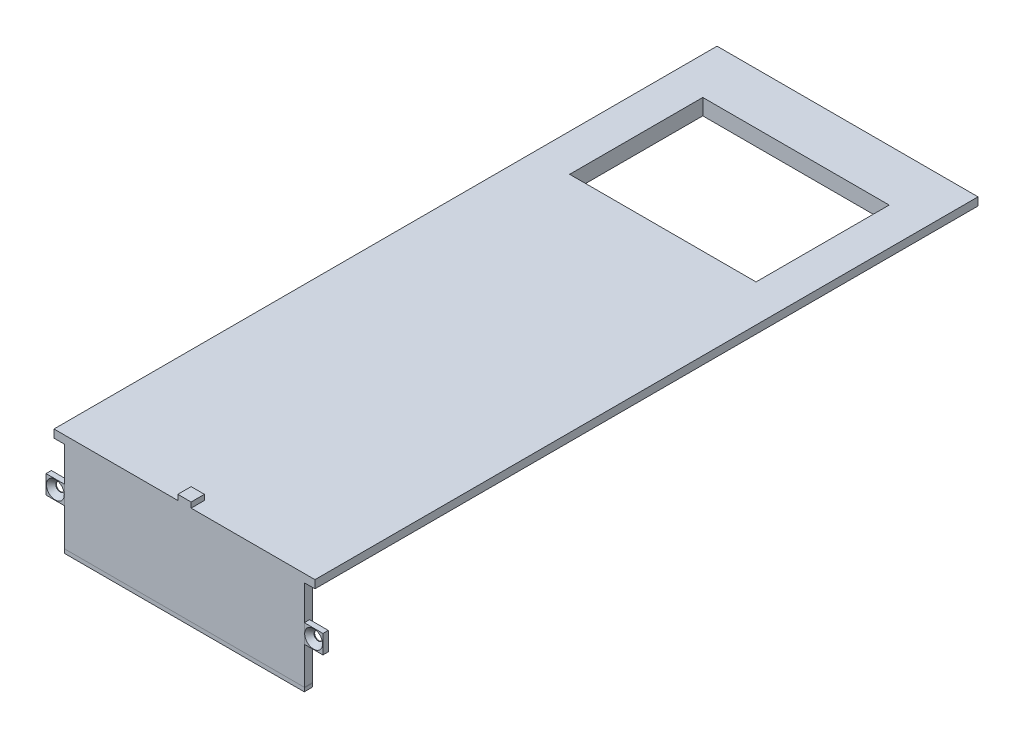
SolidWorks part; units mm, degrees
ref_plane "Front Plane" through (0, 0, 0) normal (0, 0, 1) x (1, 0, 0)
ref_plane "Top Plane" through (0, 0, 0) normal (0, 1, 0) x (1, 0, 0)
ref_plane "Right Plane" through (0, 0, 0) normal (1, 0, 0) x (0, 0, -1)
sketch "Sketch2" plane through (0, 0, 0) normal (0, 0, 1) x (1, 0, 0)
  line L0 (-50, 0) -> (50, 0)
  line L1 (50, 0) -> (50, -4)
  line L2 (50, -4) -> (45, -4)
  line L3 (45, -4) -> (45, -6)
  line L4 (45, -6) -> (-45, -6)
  line L5 (-45, -6) -> (-45, -4)
  line L6 (-45, -4) -> (-50, -4)
  line L7 (-50, -4) -> (-50, 0)
  dimension "D1" = 100
  dimension "D2" = 90
  dimension "D3" = 5
  dimension "D4" = 4
  dimension "D5" = 4
  dimension "D6" = 2
extrude "Boss-Extrude1" add sketch "Sketch2" against normal blind 249 contours L4 L5 L6 L7 L0 L1 L2 L3
sketch "Sketch4" plane through (0, -6, 0) normal (0, -1, 0) x (1, 0, 0)
  line L0 (45, -249) -> (45, 0) construction
  line L1 (-45, 0) -> (45, 0)
  line L2 (-45, 0) -> (-45, -3)
  line L3 (-45, -3) -> (45, -3)
  line L4 (45, 0) -> (45, -3)
  dimension "D1" = 3
extrude "Boss-Extrude2" add sketch "Sketch4" along normal blind 31
sketch "Sketch5" plane through (0, 0, 0) normal (0, 1, 0) x (1, 0, 0)
  line L0 (50, 249) -> (50, 0) construction
  line L1 (-35, 229.6455) -> (35, 229.6455)
  line L2 (-35, 229.6455) -> (-35, 179.6455)
  line L3 (-35, 179.6455) -> (35, 179.6455)
  line L4 (35, 229.6455) -> (35, 179.6455)
  dimension "D1" = 70
  dimension "D2" = 50
  dimension "D3" = 15
extrude "Cut-Extrude1" cut sketch "Sketch5" against normal blind 7
sketch "Sketch6" plane through (0, 0, 0) normal (0, 0, 1) x (1, 0, 0)
  line L1 (-45, -16) -> (-52, -16)
  line L2 (-45, -16) -> (-45, -23)
  line L3 (-45, -23) -> (-52, -23)
  line L4 (-52, -16) -> (-52, -23)
  line L7 (45, -16) -> (52, -16)
  line L8 (45, -16) -> (45, -23)
  line L10 (52, -16) -> (52, -23)
  line L11 (45, -23) -> (52, -23)
  line L12 (45, -4) -> (45, -37) construction
  line L13 (50, -4) -> (45, -4) construction
  line L15 (-45, -4) -> (-50, -4) construction
  line L16 (-45, -37) -> (-45, -4) construction
  circle A0 centre (-48.5, -19.5) radius 1.6
  circle A1 centre (48.5, -19.5) radius 1.6
  point P4 (0, 0)
  point P5 (0, 0)
  point P6 (0, 0)
  point P7 (0, 0)
  point P22 (0, 0)
  point P23 (0, 0)
  point P24 (49.5752, -18.9077)
  point P25 (50.0048, -19.139)
  point P32 (0, 0)
  dimension "D3" = 3.5
  dimension "D7" = 3.2
  dimension "D8" = 3.5
  dimension "D11" = 3.5
  dimension "D2" = 12
  dimension "D4" = 7
  dimension "D5" = 7
  dimension "D6" = 7
  dimension "D9" = 7
  dimension "D10" = 12
  dimension "D12" = 0
extrude "Boss-Extrude3" add sketch "Sketch6" against normal blind 2 separate body
sketch "Sketch7" plane through (0, 0, 0) normal (0, 0, 1) x (1, 0, 0)
  line L2 (-45, -37) -> (-45, -38.5009)
  line L4 (44.9879, -38.5009) -> (44.9879, -37.2504)
  line L7 (-45, -38.5009) -> (44.9879, -38.5009)
  line L8 (45, -37) -> (44.9879, -37.2504)
  line L9 (45, -37) -> (-45, -37)
  dimension "D1" = 1.5009
  dimension "D2" = 1.2505
extrude "Boss-Extrude4" add sketch "Sketch7" against normal blind 3 separate body
sketch "Sketch8" plane through (0, 0, 0) normal (0, 1, 0) x (1, 0, 0)
  line L0 (-50, 0) -> (50, 0) construction
  line L1 (-2.5, 0) -> (2.5, 0)
  line L2 (-2.5, 0) -> (-2.5, 5)
  line L3 (-2.5, 5) -> (2.5, 5)
  line L4 (2.5, 0) -> (2.5, 5)
  dimension "D1" = 5
  dimension "D2" = 5
  dimension "D3" = 2.5
extrude "Boss-Extrude5" add sketch "Sketch8" along normal blind 2
sketch "Sketch9" plane through (0, 0, 0) normal (0, 0, 1) x (1, 0, 0)
  line L0 (-49, 0) -> (-49, -3)
  line L1 (-50, 0) -> (-2.5, 0) construction
  line L2 (-49, -3) -> (-45, -3)
  line L3 (-45, -3) -> (-45, -4)
  line L4 (-45, -4) -> (-50, -4)
  line L5 (-45, -4) -> (-50, -4) construction
  line L6 (-50, -4) -> (-50, 0) construction
  line L7 (-50, -4) -> (-50, 0)
  line L8 (-50, 0) -> (-49, 0)
  line L9 (49, 0) -> (50, 0)
  line L10 (2.5, 0) -> (50, 0) construction
  line L11 (50, 0) -> (50, -4)
  line L12 (50, -4) -> (45, -4)
  line L13 (45, -4) -> (45, -3)
  line L14 (45, -3) -> (49, -3)
  line L15 (49, -3) -> (49, 0)
  dimension "D1" = 1
  dimension "D2" = 1
  dimension "D3" = 1
  dimension "D4" = 1
extrude "Cut-Extrude2" cut sketch "Sketch9" against normal through all
hole_wizard "CSK for M3 Hex Socket Countersunk Cap Screw1" positions "Sketch12" profile "Sketch13" countersink size "M3" standard "ISO"
sketch "Sketch12" plane through (0, 0, 0) normal (0, 0, 1) x (1, 0, 0)
  point P0 (-48.5, -19.5)
  point P3 (48.5, -19.5)
sketch "Sketch13" plane through (-48.5, -19.5, 0) normal (1, 0, 0) x (0, -1, 0)
  line L0 (0, 0) -> (0, 6.2)
  line L1 (0, 6.2) -> (1.6, 5.2386)
  line L2 (1.6, 5.2386) -> (1.6, 1.76)
  line L3 (1.6, 1.76) -> (3.36, 0)
  line L5 (3.36, 0) -> (0, 0)
  line L6 (-1.6, 1.76) -> (-3.36, 0) construction
  line L10 (0, 6.2) -> (-1.6, 5.2386) construction
  line L11 (0, -6.35) -> (0, 107.95) construction
  dimension "Hole Dia." = 3.2
  dimension "Hole Depth" = 6.2
  dimension "Near C'Sink Dia." = 6.72
  dimension "Near C'Sink Angle" = 90
  dimension "Drill Angle" = 118
